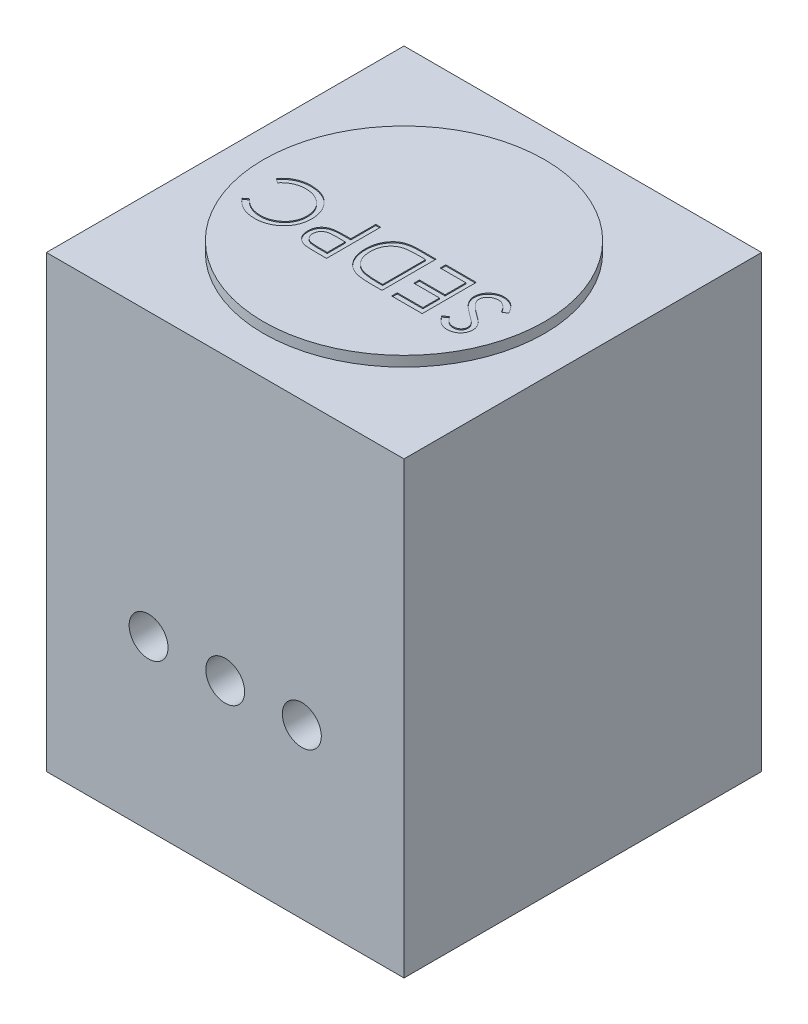
SolidWorks part; units mm, degrees
ref_plane "Alzado" through (0, 0, 0) normal (0, 0, 1) x (1, 0, 0)
ref_plane "Planta" through (0, 0, 0) normal (0, 1, 0) x (1, 0, 0)
ref_plane "Vista lateral" through (0, 0, 0) normal (1, 0, 0) x (0, 0, -1)
sketch "Croquis1" plane through (0, 0, 0) normal (0, 1, 0) x (1, 0, 0)
  line L1 (-350, 350) -> (350, 350)
  line L2 (-350, 350) -> (-350, -350)
  line L3 (-350, -350) -> (350, -350)
  line L4 (350, 350) -> (350, -350)
  line L5 (-350, 350) -> (350, -350) construction
  line L6 (-350, -350) -> (350, 350) construction
  point P0 (0, 0)
  dimension "D1" = 700
  dimension "D2" = 700
extrude "Saliente-Extruir1" add sketch "Croquis1" along normal blind 900
sketch "Croquis2" plane through (0, 900, 0) normal (0, 1, 0) x (1, 0, 0)
  line L1 (-350, -350) -> (350, -350)
  line L2 (-350, -350) -> (-350, 350)
  line L3 (-350, 350) -> (350, 350)
  line L4 (350, -350) -> (350, 350)
  line L5 (-350, -350) -> (350, 350) construction
  line L6 (-350, 350) -> (350, -350) construction
  circle A0 centre (0, 0) radius 275
  dimension "D1" = 550
extrude "Cortar-Extruir1" cut sketch "Croquis2" against normal blind 20
sketch "Croquis3" plane through (0, 900, 0) normal (0, 1, 0) x (1, 0, 0)
  line L0 (249.4965, 0) -> (-259.6283, 0) construction
  text T0 "SEDPC" font "Century Gothic" height in points 400
extrude "Cortar-Extruir2" cut sketch "Croquis3" against normal blind 2
sketch "Croquis4" plane through (0, 0, 350) normal (0, 0, 1) x (1, 0, 0)
  line L0 (0, 0) -> (0, 328.97) construction
  line L1 (0, 328.97) -> (-150, 328.97) construction
  circle A0 centre (0, 328.97) radius 38.1
  circle A1 centre (-150, 328.97) radius 38.1
  circle A2 centre (150, 328.97) radius 38.1
  dimension "D1" = 76.2
  dimension "D3" = 76.2
  dimension "D2" = 150
extrude "Cortar-Extruir3" cut sketch "Croquis4" against normal blind 94
